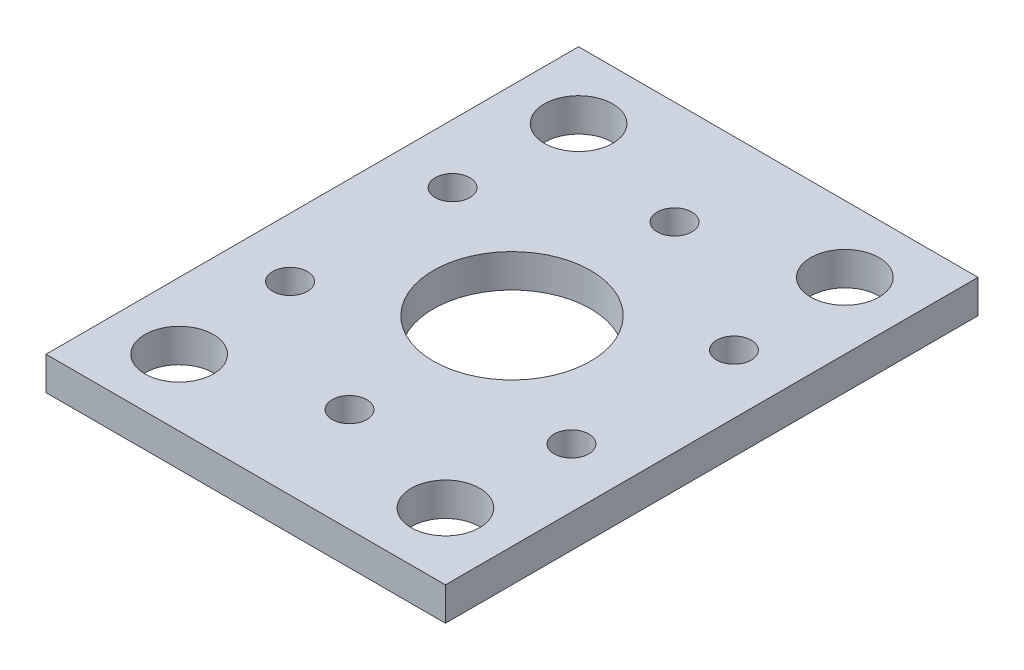
SolidWorks part; units mm, degrees
ref_plane "Front Plane" through (0, 0, 0) normal (0, 0, 1) x (1, 0, 0)
ref_plane "Top Plane" through (0, 0, 0) normal (0, 1, 0) x (1, 0, 0)
ref_plane "Right Plane" through (0, 0, 0) normal (1, 0, 0) x (0, 0, -1)
sketch "Sketch1" plane through (0, 0, 0) normal (0, 1, 0) x (1, 0, 0)
  line L0 (0, -50.8) -> (0, 0)
  line L1 (0, 0) -> (38.1, 0)
  line L2 (38.1, 0) -> (38.1, -50.8)
  line L3 (0, -50.8) -> (38.1, -50.8)
  circle A1 centre (19.05, -40.9) radius 1.65
  circle A2 centre (5.6266, -33.15) radius 1.65
  circle A3 centre (5.6266, -17.65) radius 1.65
  circle A4 centre (19.05, -9.9) radius 1.65
  circle A5 centre (32.4734, -17.65) radius 1.65
  circle A6 centre (32.4734, -33.15) radius 1.65
  circle A7 centre (19.05, -25.4) radius 7.5
  circle A8 centre (6.35, -6.35) radius 3.2639
  circle A9 centre (31.75, -6.35) radius 3.2639
  circle A10 centre (6.35, -44.45) radius 3.2639
  circle A11 centre (31.75, -44.45) radius 3.2639
  point P20 (19.05, -25.4)
  point P27 (0, 0)
  point P28 (0, 0)
  dimension "D1" = 3.3
  dimension "D5" = 15
  dimension "D6" = 6.5278
  dimension "D2" = 15.5
  dimension "D3" = 38.1
  dimension "D7" = 6.35
  dimension "D8" = 6.35
  dimension "D9" = 6.35
  dimension "D10" = 25.4
  dimension "D11" = 50.8
  dimension "D12" = 6.35
  dimension "D13" = 6.35
  dimension "D4" = 6
extrude "Base Extrude" add sketch "Sketch1" along normal blind 3.175
